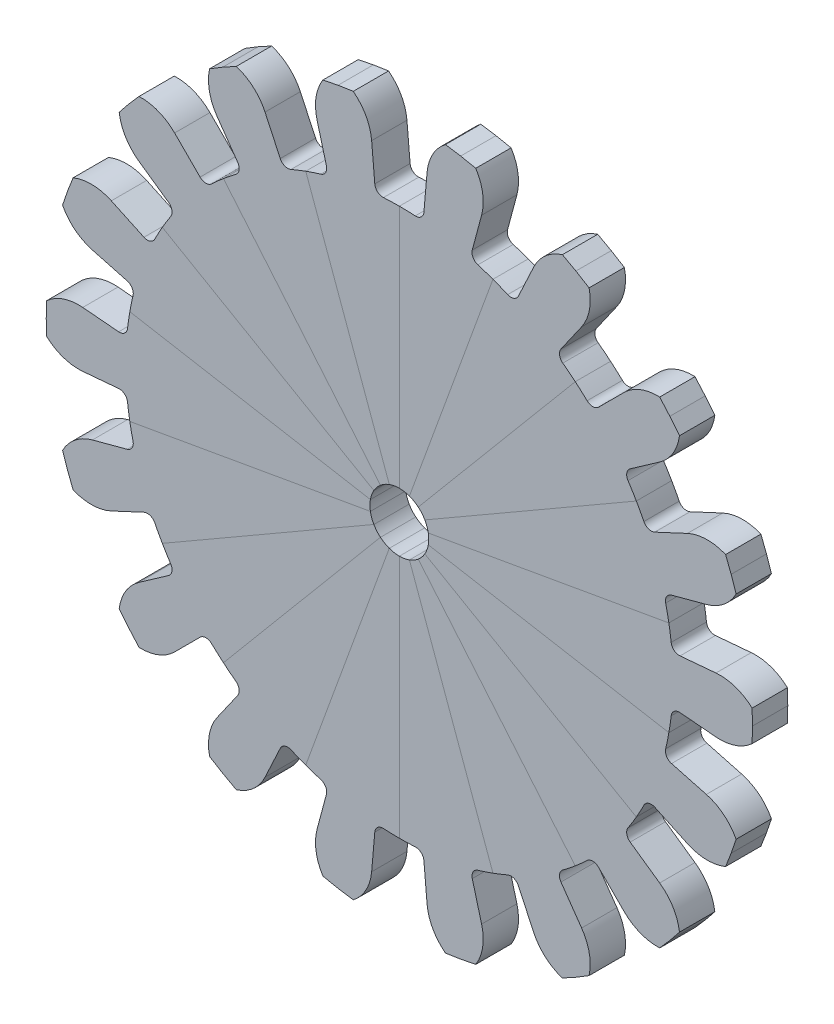
SolidWorks part; units mm, degrees
ref_plane "Plan de face" through (0, 0, 0) normal (0, 0, 1) x (1, 0, 0)
ref_plane "Plan de dessus" through (0, 0, 0) normal (0, 1, 0) x (1, 0, 0)
ref_plane "Plan de droite" through (0, 0, 0) normal (1, 0, 0) x (0, 0, -1)
sketch "Esquisse4" plane through (0, 0, 0) normal (0, 0, 1) x (1, 0, 0)
  line L0 (0, 0) -> (15.5601, 0) construction
  line L1 (0, 0) -> (17.2426, 1.5085) construction
  line L2 (0, 0) -> (17.0187, 3.0009) construction
  line L3 (0, 0) -> (17.2619, 0.7537) construction
  line L4 (23.1615, 2.0264) -> (26.8973, 2.3532)
  line L5 (22.8968, 4.0373) -> (0, 0)
  line L6 (29.9714, 1.3086) -> (30, 0)
  line L7 (29.9714, -1.3086) -> (30, 0)
  line L8 (23.1615, -2.0264) -> (26.8973, -2.3532)
  line L9 (22.8968, -4.0373) -> (0, 0)
  circle A0 centre (0, 0) radius 23.25 construction
  circle A1 centre (0, 0) radius 27 construction
  circle A2 centre (0, 0) radius 30 construction
  arc A3 (29.9714, 1.3086) -> (26.8973, 2.3532) centre (27.2483, -1.6594) ccw
  arc A4 (23.1615, 2.0264) -> (22.8968, 4.0373) centre (0, 0) ccw
  arc A5 (29.9714, -1.3086) -> (26.8973, -2.3532) centre (27.2483, 1.6594) cw
  arc A6 (23.1615, -2.0264) -> (22.8968, -4.0373) centre (0, 0) cw
  dimension "D1" = 60
  dimension "D2" = 54
  dimension "D3" = 46.5
  dimension "D4" = 10
  dimension "D5" = 5
  dimension "D6" = 2.5
extrude "Boss.-Extru.4" add sketch "Esquisse4" along normal blind 3 contours A6 L8 A5 L7 L6 A3 L4 A4 L5 L9
fillet "Congé1" radius 0.7 2 edges at (23.1615, 2.0264, 1.5) (23.1615, -2.0264, 1.5)
pattern_circular "Répétition circulaire1" count 18 over 360 about axis through (0, 0, 0) along (0, 0, 1) of bodies 103
sketch "Esquisse5" plane through (0, 0, 0) normal (0, 0, -1) x (-1, 0, 0)
  circle A0 centre (0, 0) radius 2.5
  dimension "D1" = 5
extrude "Enlèv. mat.-Extru.1" cut sketch "Esquisse5" against normal through all
